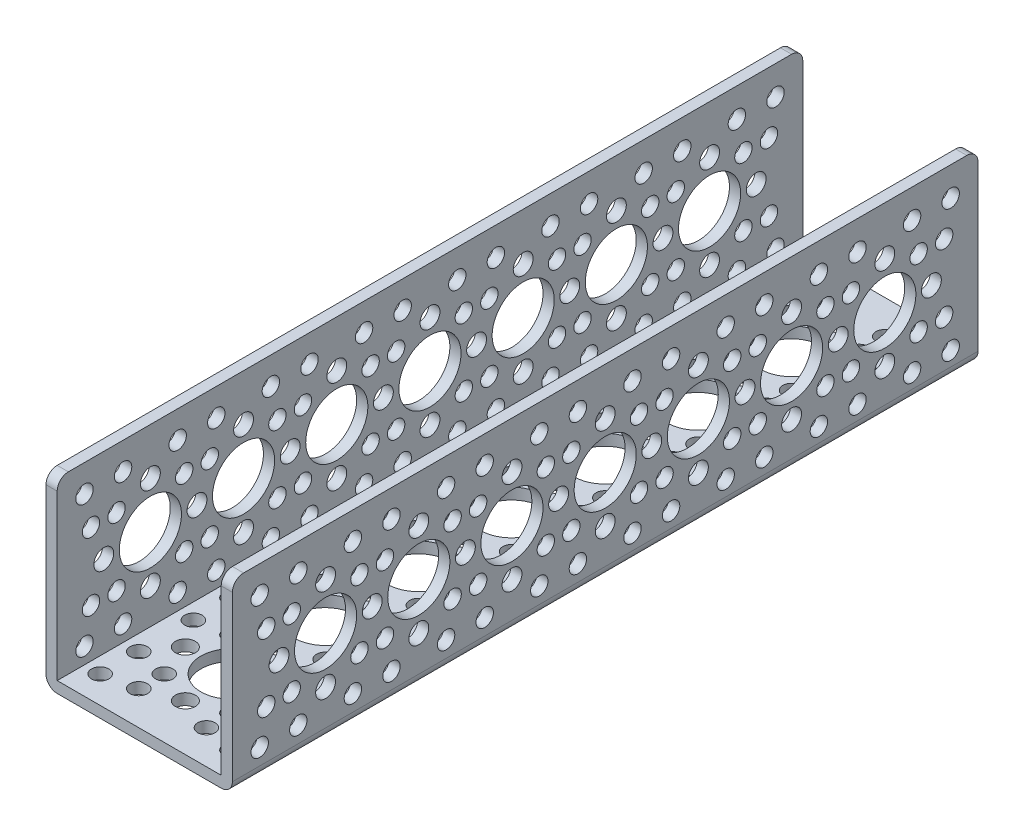
SolidWorks part; units mm, degrees
ref_plane "Front Plane" through (0, 0, 0) normal (0, 0, 1) x (1, 0, 0)
ref_plane "Top Plane" through (0, 0, 0) normal (0, 1, 0) x (1, 0, 0)
ref_plane "Right Plane" through (0, 0, 0) normal (1, 0, 0) x (0, 0, -1)
sketch "Sketch1" plane through (0, 0, 0) normal (0, 0, 1) x (1, 0, 0)
  line L1 (0, 0) -> (38.1, 0)
  line L2 (0, 0) -> (0, 38.1)
  line L4 (38.1, 0) -> (38.1, 38.1)
extrude "Extrude-Thin1" add sketch "Sketch1" along normal blind 152.4 thin thin type one direction wall 2.286
sketch "Sketch3" plane through (0, 0, 0) normal (0, -1, 0) x (1, 0, 0)
  line L0 (38.1, 0) -> (0, 0) construction
  circle B0 centre (19.05, 19.0584) radius 6.35
  circle B1 centre (19.05, 9.5334) radius 2.032
  circle B2 centre (9.525, 19.0584) radius 2.032
  circle B3 centre (19.05, 28.5834) radius 2.032
  circle B4 centre (28.575, 19.0584) radius 2.032
  circle B5 centre (12.1352, 25.9732) radius 1.778
  circle B6 centre (5.5796, 32.5288) radius 1.778
  circle B7 centre (25.9648, 25.9732) radius 1.778
  circle B8 centre (32.5204, 32.5288) radius 1.778
  circle B9 centre (25.9648, 12.1436) radius 1.778
  circle B10 centre (32.5204, 5.588) radius 1.778
  circle B11 centre (12.1352, 12.1436) radius 1.778
  circle B12 centre (5.5796, 5.588) radius 1.778
  circle B13 centre (12.1352, 31.1936) radius 1.778
  circle B14 centre (25.9648, 31.1936) radius 1.778
  circle B15 centre (25.9648, 6.9232) radius 1.778
  circle B16 centre (12.1352, 6.9232) radius 1.778
  circle B17 centre (32.5204, 13.4788) radius 1.778
  circle B18 centre (5.5796, 13.4788) radius 1.778
  circle B19 centre (5.5796, 24.638) radius 1.778
  circle B20 centre (32.5204, 24.638) radius 1.778
  circle B21 centre (18.9713, 38.1084) radius 6.35
  circle B22 centre (9.4463, 38.1084) radius 2.032
  circle B23 centre (28.4963, 38.1084) radius 2.032
  circle B24 centre (18.9713, 57.1584) radius 6.35
  circle B25 centre (18.9713, 47.6334) radius 2.032
  circle B26 centre (9.4463, 57.1584) radius 2.032
  circle B27 centre (18.9713, 66.6834) radius 2.032
  circle B28 centre (28.4963, 57.1584) radius 2.032
  circle B29 centre (12.0565, 64.0732) radius 1.778
  circle B30 centre (5.5009, 70.6288) radius 1.778
  circle B31 centre (25.8861, 64.0732) radius 1.778
  circle B32 centre (32.4417, 70.6288) radius 1.778
  circle B33 centre (25.8861, 50.2436) radius 1.778
  circle B34 centre (32.4417, 43.688) radius 1.778
  circle B35 centre (12.0565, 50.2436) radius 1.778
  circle B36 centre (5.5009, 43.688) radius 1.778
  circle B37 centre (12.0565, 69.2936) radius 1.778
  circle B38 centre (25.8861, 69.2936) radius 1.778
  circle B39 centre (25.8861, 45.0232) radius 1.778
  circle B40 centre (12.0565, 45.0232) radius 1.778
  circle B41 centre (32.4417, 51.5788) radius 1.778
  circle B42 centre (5.5009, 51.5788) radius 1.778
  circle B43 centre (5.5009, 62.738) radius 1.778
  circle B44 centre (32.4417, 62.738) radius 1.778
  circle B45 centre (18.9713, 76.2084) radius 6.35
  circle B46 centre (9.4463, 76.2084) radius 2.032
  circle B47 centre (28.4963, 76.2084) radius 2.032
  circle B48 centre (18.9713, 95.2584) radius 6.35
  circle B49 centre (18.9713, 85.7334) radius 2.032
  circle B50 centre (9.4463, 95.2584) radius 2.032
  circle B51 centre (18.9713, 104.7834) radius 2.032
  circle B52 centre (28.4963, 95.2584) radius 2.032
  circle B53 centre (12.0565, 102.1732) radius 1.778
  circle B54 centre (5.5009, 108.7288) radius 1.778
  circle B55 centre (25.8861, 102.1732) radius 1.778
  circle B56 centre (32.4417, 108.7288) radius 1.778
  circle B57 centre (25.8861, 88.3436) radius 1.778
  circle B58 centre (32.4417, 81.788) radius 1.778
  circle B59 centre (12.0565, 88.3436) radius 1.778
  circle B60 centre (5.5009, 81.788) radius 1.778
  circle B61 centre (12.0565, 107.3936) radius 1.778
  circle B62 centre (25.8861, 107.3936) radius 1.778
  circle B63 centre (25.8861, 83.1232) radius 1.778
  circle B64 centre (12.0565, 83.1232) radius 1.778
  circle B65 centre (32.4417, 89.6788) radius 1.778
  circle B66 centre (5.5009, 89.6788) radius 1.778
  circle B67 centre (5.5009, 100.838) radius 1.778
  circle B68 centre (32.4417, 100.838) radius 1.778
  circle B69 centre (18.9713, 133.3584) radius 6.35
  circle B70 centre (18.9713, 123.8334) radius 2.032
  circle B71 centre (9.4463, 133.3584) radius 2.032
  circle B72 centre (18.9713, 142.8834) radius 2.032
  circle B73 centre (28.4963, 133.3584) radius 2.032
  circle B74 centre (12.0565, 140.2732) radius 1.778
  circle B75 centre (5.5009, 146.8288) radius 1.778
  circle B76 centre (25.8861, 140.2732) radius 1.778
  circle B77 centre (32.4417, 146.8288) radius 1.778
  circle B78 centre (25.8861, 126.4436) radius 1.778
  circle B79 centre (32.4417, 119.888) radius 1.778
  circle B80 centre (12.0565, 126.4436) radius 1.778
  circle B81 centre (5.5009, 119.888) radius 1.778
  circle B82 centre (12.0565, 145.4936) radius 1.778
  circle B83 centre (25.8861, 145.4936) radius 1.778
  circle B84 centre (25.8861, 121.2232) radius 1.778
  circle B85 centre (12.0565, 121.2232) radius 1.778
  circle B86 centre (32.4417, 127.7788) radius 1.778
  circle B87 centre (5.5009, 127.7788) radius 1.778
  circle B88 centre (5.5009, 138.938) radius 1.778
  circle B89 centre (32.4417, 138.938) radius 1.778
  circle B90 centre (18.9713, 114.3084) radius 6.35
  circle B91 centre (9.4463, 114.3084) radius 2.032
  circle B92 centre (28.4963, 114.3084) radius 2.032
  dimension "D1" = 19.05
  dimension "D2" = 38.1
  dimension "D3" = 5.588
  dimension "D4" = 19.05
  dimension "D5" = 38.1
sketch_block_instance "actobotics hole pattern-2"
sketch_block "actobotics hole pattern" parameters "D1"=12.7, "D3"=4.064, "D6"=3.556, "D7"=3.556, "D2"=9.525, "D4"=19.05, "D5"=9.779
sketch_block_instance "Actobotics hole pattern c-6"
sketch_block "Actobotics hole pattern c" parameters "D1"=12.7, "D4"=4.064, "D2"=19.05, "D3"=9.525
sketch_block_instance "actobotics hole pattern-1"
sketch_block_instance "Actobotics hole pattern c-9"
sketch_block_instance "actobotics hole pattern-9"
sketch_block_instance "actobotics hole pattern-11"
sketch_block_instance "Actobotics hole pattern c-11"
extrude "Cut-Extrude1" cut sketch "Sketch3" against normal up to next (2.286 mm away)
sketch "Sketch4" plane through (0, 0, 0) normal (-1, 0, 0) x (0, 0, 1)
  line L0 (0, 19.05) -> (152.4, 19.05) construction
  line L1 (0, 0) -> (0, 38.1) construction
  line L3 (152.4, 0) -> (152.4, 38.1) construction
  circle B0 centre (114.3, 19.05) radius 6.35
  circle B1 centre (114.3, 9.525) radius 2.032
  circle B2 centre (114.3, 28.575) radius 2.032
  circle B3 centre (95.25, 19.05) radius 6.35
  circle B4 centre (104.775, 19.0494) radius 2.032
  circle B5 centre (95.2494, 9.525) radius 2.032
  circle B6 centre (85.725, 19.0506) radius 2.032
  circle B7 centre (95.2506, 28.575) radius 2.032
  circle B8 centre (88.3348, 12.1356) radius 1.778
  circle B9 centre (81.7788, 5.5804) radius 1.778
  circle B10 centre (88.3356, 25.9652) radius 1.778
  circle B11 centre (81.7804, 32.5212) radius 1.778
  circle B12 centre (102.1652, 25.9644) radius 1.778
  circle B13 centre (108.7212, 32.5196) radius 1.778
  circle B14 centre (102.1644, 12.1348) radius 1.778
  circle B15 centre (108.7196, 5.5788) radius 1.778
  circle B16 centre (83.1144, 12.1359) radius 1.778
  circle B17 centre (83.1152, 25.9655) radius 1.778
  circle B18 centre (107.3856, 25.9641) radius 1.778
  circle B19 centre (107.3848, 12.1345) radius 1.778
  circle B20 centre (100.8304, 32.5201) radius 1.778
  circle B21 centre (100.8288, 5.5793) radius 1.778
  circle B22 centre (89.6696, 5.5799) radius 1.778
  circle B23 centre (89.6712, 32.5207) radius 1.778
  circle B24 centre (133.35, 19.05) radius 6.35
  circle B25 centre (142.875, 19.05) radius 2.032
  circle B26 centre (133.35, 9.525) radius 2.032
  circle B27 centre (123.825, 19.05) radius 2.032
  circle B28 centre (133.35, 28.575) radius 2.032
  circle B29 centre (126.4352, 12.1352) radius 1.778
  circle B30 centre (119.8796, 5.5796) radius 1.778
  circle B31 centre (126.4352, 25.9648) radius 1.778
  circle B32 centre (119.8796, 32.5204) radius 1.778
  circle B33 centre (140.2648, 25.9648) radius 1.778
  circle B34 centre (146.8204, 32.5204) radius 1.778
  circle B35 centre (140.2648, 12.1352) radius 1.778
  circle B36 centre (146.8204, 5.5796) radius 1.778
  circle B37 centre (121.2148, 12.1352) radius 1.778
  circle B38 centre (121.2148, 25.9648) radius 1.778
  circle B39 centre (145.4852, 25.9648) radius 1.778
  circle B40 centre (145.4852, 12.1352) radius 1.778
  circle B41 centre (138.9296, 32.5204) radius 1.778
  circle B42 centre (138.9296, 5.5796) radius 1.778
  circle B43 centre (127.7704, 5.5796) radius 1.778
  circle B44 centre (127.7704, 32.5204) radius 1.778
  circle B45 centre (76.2002, 18.965) radius 6.35
  circle B46 centre (76.2002, 9.44) radius 2.032
  circle B47 centre (76.2002, 28.49) radius 2.032
  circle B48 centre (57.1504, 18.8801) radius 6.35
  circle B49 centre (66.6754, 18.8795) radius 2.032
  circle B50 centre (57.1498, 9.3551) radius 2.032
  circle B51 centre (47.6254, 18.8806) radius 2.032
  circle B52 centre (57.1509, 28.4051) radius 2.032
  circle B53 centre (50.2352, 11.9657) radius 1.778
  circle B54 centre (43.6792, 5.4105) radius 1.778
  circle B55 centre (50.236, 25.7953) radius 1.778
  circle B56 centre (43.6808, 32.3513) radius 1.778
  circle B57 centre (64.0656, 25.7944) radius 1.778
  circle B58 centre (70.6216, 32.3496) radius 1.778
  circle B59 centre (64.0648, 11.9649) radius 1.778
  circle B60 centre (70.62, 5.4089) radius 1.778
  circle B61 centre (45.0148, 11.966) radius 1.778
  circle B62 centre (45.0156, 25.7956) radius 1.778
  circle B63 centre (69.286, 25.7941) radius 1.778
  circle B64 centre (69.2852, 11.9645) radius 1.778
  circle B65 centre (62.7308, 32.3501) radius 1.778
  circle B66 centre (62.7292, 5.4093) radius 1.778
  circle B67 centre (51.57, 5.41) radius 1.778
  circle B68 centre (51.5716, 32.3508) radius 1.778
  circle B69 centre (38.1006, 18.7951) radius 6.35
  circle B70 centre (38.1006, 9.2701) radius 2.032
  circle B71 centre (38.1006, 28.3201) radius 2.032
  circle B72 centre (19.0508, 18.7101) radius 6.35
  circle B73 centre (28.5758, 18.7096) radius 2.032
  circle B74 centre (19.0502, 9.1851) radius 2.032
  circle B75 centre (9.5258, 18.7107) radius 2.032
  circle B76 centre (19.0513, 28.2351) radius 2.032
  circle B77 centre (12.1355, 11.7957) radius 1.778
  circle B78 centre (5.5796, 5.2406) radius 1.778
  circle B79 centre (12.1364, 25.6253) radius 1.778
  circle B80 centre (5.5812, 32.1813) radius 1.778
  circle B81 centre (25.966, 25.6245) radius 1.778
  circle B82 centre (32.5219, 32.1797) radius 1.778
  circle B83 centre (25.9651, 11.7949) radius 1.778
  circle B84 centre (32.5203, 5.2389) radius 1.778
  circle B85 centre (6.9151, 11.7961) radius 1.778
  circle B86 centre (6.916, 25.6257) radius 1.778
  circle B87 centre (31.1864, 25.6242) radius 1.778
  circle B88 centre (31.1855, 11.7946) radius 1.778
  circle B89 centre (24.6312, 32.1802) radius 1.778
  circle B90 centre (24.6296, 5.2394) radius 1.778
  circle B91 centre (13.4703, 5.2401) radius 1.778
  circle B92 centre (13.4719, 32.1808) radius 1.778
  dimension "D1" = 19.05
  dimension "D2" = 38.1
  dimension "D3" = 5.5796
  dimension "D4" = 19.05
  dimension "D5" = 38.1
sketch_block_instance "Actobotics hole pattern c-7"
sketch_block_instance "actobotics hole pattern-6"
sketch_block_instance "actobotics hole pattern-7"
sketch_block_instance "Actobotics hole pattern c-8"
sketch_block_instance "actobotics hole pattern-8"
sketch_block_instance "Actobotics hole pattern c-10"
sketch_block_instance "actobotics hole pattern-10"
extrude "Cut-Extrude2" cut sketch "Sketch4" against normal through all
fillet "Fillet1" radius 2.286 6 edges at (1.143, 38.1, 152.4) (36.957, 38.1, 152.4) (36.957, 38.1, 0) (1.143, 38.1, 0) (38.1, 0, 76.2) (0, 0, 76.2)
